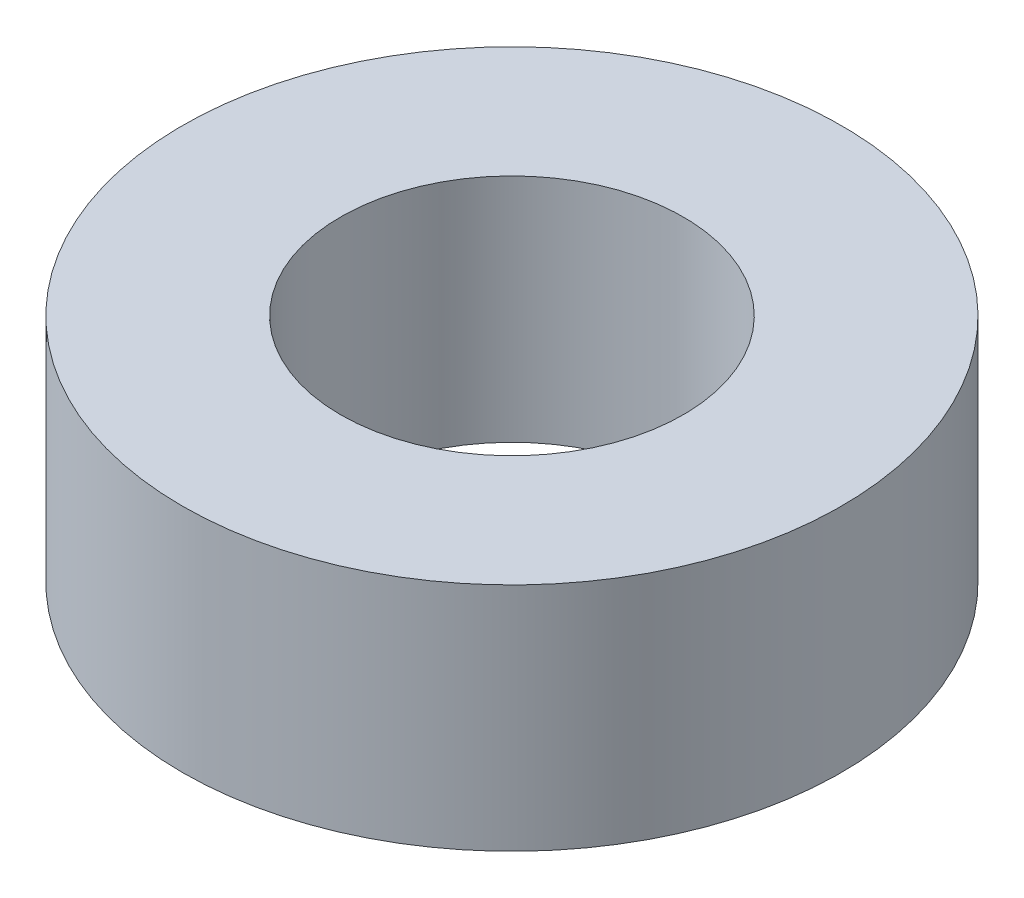
SolidWorks part; units mm, degrees
ref_plane "Front Plane" through (0, 0, 0) normal (0, 0, 1) x (1, 0, 0)
ref_plane "Top Plane" through (0, 0, 0) normal (0, 1, 0) x (1, 0, 0)
ref_plane "Right Plane" through (0, 0, 0) normal (1, 0, 0) x (0, 0, -1)
sketch "Sketch1" plane through (0, 0, 0) normal (0, 1, 0) x (1, 0, 0)
  circle A0 centre (0, 0) radius 2.6
  circle A1 centre (0, 0) radius 5
  dimension "D1" = 5.2
  dimension "D2" = 10
extrude "Boss-Extrude1" add sketch "Sketch1" along normal blind 3.5
